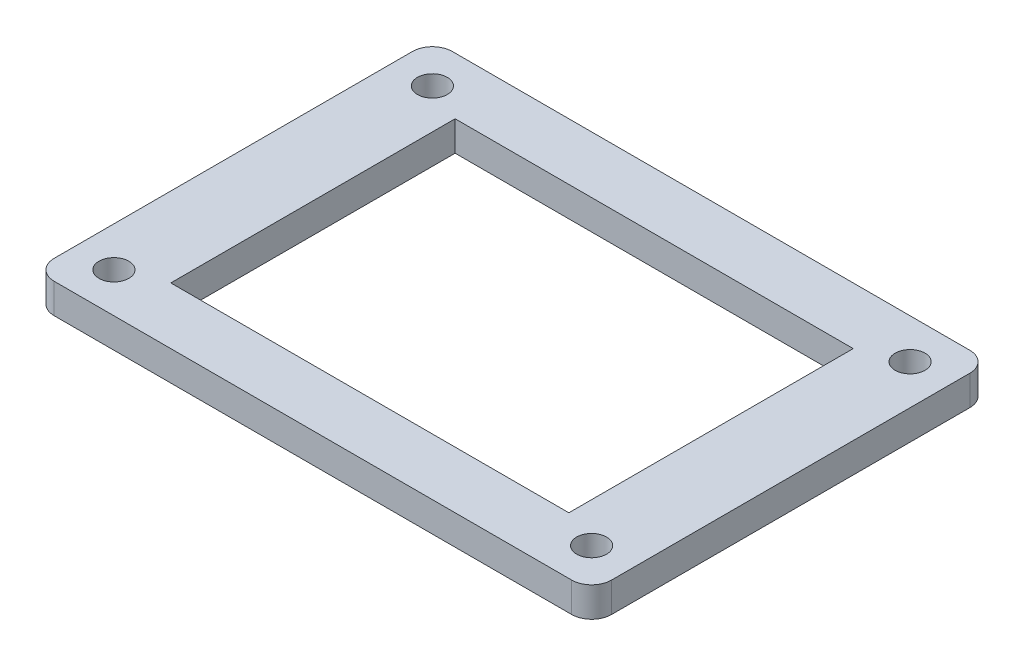
SolidWorks part; units mm, degrees
ref_plane "Front Plane" through (0, 0, 0) normal (0, 0, 1) x (1, 0, 0)
ref_plane "Top Plane" through (0, 0, 0) normal (0, 1, 0) x (1, 0, 0)
ref_plane "Right Plane" through (0, 0, 0) normal (1, 0, 0) x (0, 0, -1)
sketch "Sketch2" plane through (0, 0, 0) normal (0, 1, 0) x (1, 0, 0)
  line L1 (-28, -20) -> (28, -20)
  line L2 (-28, -20) -> (-28, 20)
  line L3 (-28, 20) -> (28, 20)
  line L4 (28, -20) -> (28, 20)
  line L5 (-28, -20) -> (28, 20) construction
  line L6 (-28, 20) -> (28, -20) construction
  line L7 (-20, -14.2857) -> (20, -14.2857)
  line L8 (-20, -14.2857) -> (-20, 14.2857)
  line L9 (-20, 14.2857) -> (20, 14.2857)
  line L10 (20, -14.2857) -> (20, 14.2857)
  line L11 (-20, -14.2857) -> (20, 14.2857) construction
  line L12 (-20, 14.2857) -> (20, -14.2857) construction
  point P0 (0, 0)
  point P6 (0, 0)
  dimension "D1" = 56
  dimension "D2" = 40
  dimension "D3" = 8
extrude "Boss-Extrude2" add sketch "Sketch2" along normal blind 3
sketch "Sketch3" plane through (0, 0, 0) normal (0, -1, 0) x (-1, 0, 0)
  circle A0 centre (24, -16) radius 1.5
  circle A1 centre (-24, 16) radius 1.5
  circle A2 centre (-24, -16) radius 1.5
  circle A4 centre (24, 16) radius 1.5
  dimension "D1" = 3
  dimension "D2" = 3
  dimension "D3" = 3
  dimension "D4" = 3
extrude "Cut-Extrude1" cut sketch "Sketch3" against normal through all
fillet "Fillet1" radius 2 4 edges at (28, 1.5, 20) (28, 1.5, -20) (-28, 1.5, -20) (-28, 1.5, 20)
